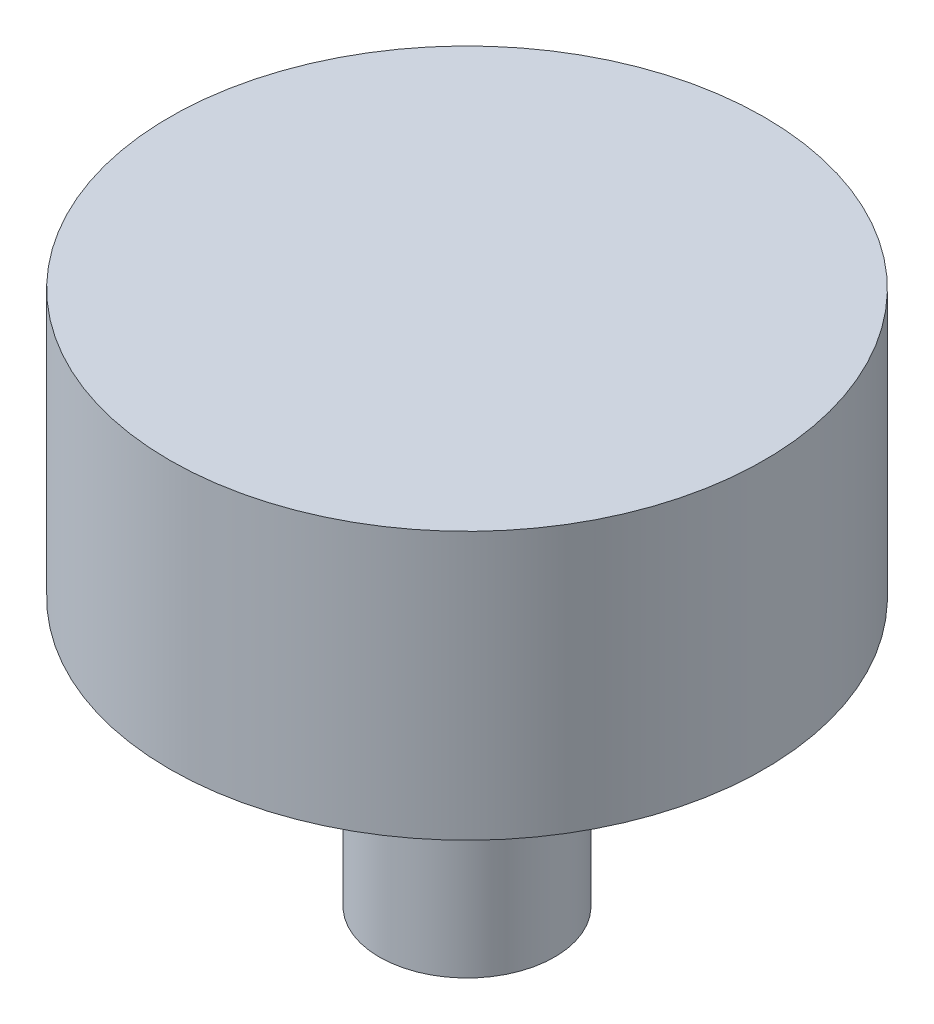
SolidWorks part; units mm, degrees
ref_plane "Front Plane" through (0, 0, 0) normal (0, 0, 1) x (1, 0, 0)
ref_plane "Top Plane" through (0, 0, 0) normal (0, 1, 0) x (1, 0, 0)
ref_plane "Right Plane" through (0, 0, 0) normal (1, 0, 0) x (0, 0, -1)
sketch "Sketch1" plane through (0, 0, 0) normal (0, 1, 0) x (1, 0, 0)
  circle A0 centre (0, 0) radius 2.2
  circle A1 centre (0, 0) radius 2.95
  dimension "D1" = 4.4
  dimension "D2" = 5.9
extrude "Boss-Extrude1" add sketch "Sketch1" along normal blind 9
sketch "Sketch2" plane through (0, 9, 0) normal (0, 1, 0) x (1, 0, 0)
  circle A0 centre (0, 0) radius 10
  dimension "D1" = 20
extrude "Boss-Extrude2" add sketch "Sketch2" along normal blind 9
